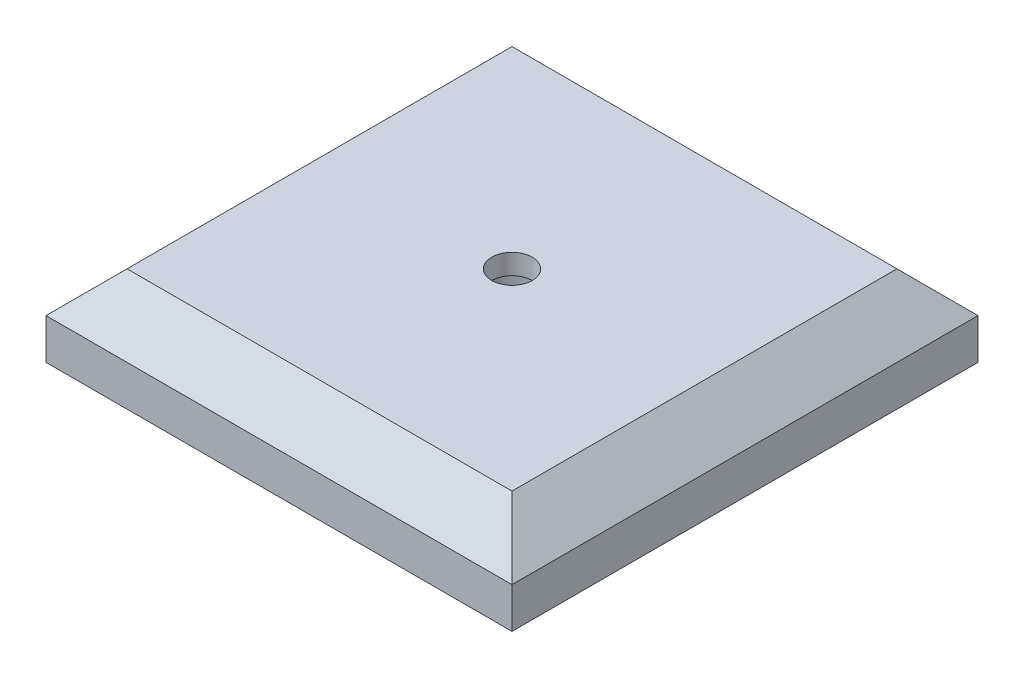
SolidWorks part; units mm, degrees
material "Plain Carbon Steel"
ref_plane "Front Plane" through (0, 0, 0) normal (0, 0, 1) x (1, 0, 0)
ref_plane "Top Plane" through (0, 0, 0) normal (0, 1, 0) x (1, 0, 0)
ref_plane "Right Plane" through (0, 0, 0) normal (1, 0, 0) x (0, 0, -1)
sketch "Sketch1" plane through (0, 0, 0) normal (0, 1, 0) x (1, 0, 0)
  line L1 (-36.5125, -36.5125) -> (36.5125, -36.5125)
  line L2 (-36.5125, -36.5125) -> (-36.5125, 36.5125)
  line L3 (-36.5125, 36.5125) -> (36.5125, 36.5125)
  line L4 (36.5125, -36.5125) -> (36.5125, 36.5125)
  line L5 (-36.5125, -36.5125) -> (36.5125, 36.5125) construction
  line L6 (-36.5125, 36.5125) -> (36.5125, -36.5125) construction
  point P0 (0, 0)
  dimension "D1" = 73.025
  dimension "D2" = 73.025
extrude "Boss-Extrude1" add sketch "Sketch1" along normal blind 12.7
chamfer "Chamfer1" distance 6.35 4 edges at (0, 12.7, 36.5125) (36.5125, 12.7, 0) (0, 12.7, -36.5125) (-36.5125, 12.7, 0)
sketch "Sketch4" plane through (0, 12.7, 0) normal (0, 1, 0) x (1, 0, 0)
  circle A0 centre (0, 0) radius 3.175
  dimension "D1" = 6.35
extrude "Cut-Extrude1" cut sketch "Sketch4" against normal blind 3.175
sketch "Sketch5" plane through (0, 9.525, 0) normal (0, 1, 0) x (1, 0, 0)
  circle A0 centre (0, 0) radius 6.35
  dimension "D1" = 12.7
extrude "Cut-Extrude2" cut sketch "Sketch5" against normal up to next
